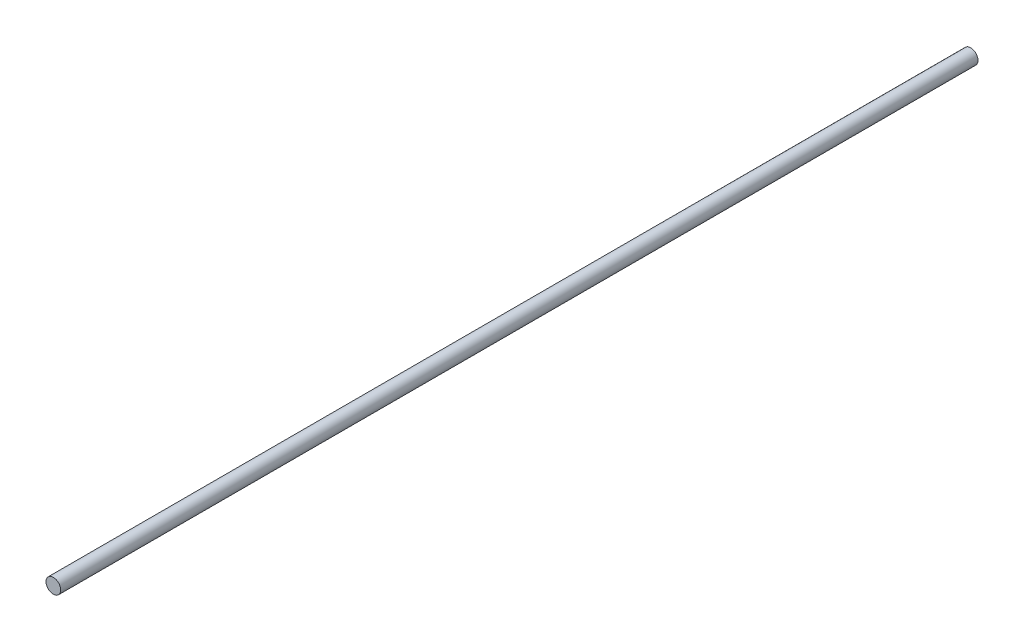
SolidWorks part; units mm, degrees
ref_plane "Front Plane" through (0, 0, 0) normal (0, 0, 1) x (1, 0, 0)
ref_plane "Top Plane" through (0, 0, 0) normal (0, 1, 0) x (1, 0, 0)
ref_plane "Right Plane" through (0, 0, 0) normal (1, 0, 0) x (0, 0, -1)
sketch "Sketch1" plane through (0, 0, 0) normal (0, 0, 1) x (1, 0, 0)
  circle A0 centre (0, 0) radius 2
  dimension "D1" = 4
extrude "Boss-Extrude1" add sketch "Sketch1" along normal blind 250
